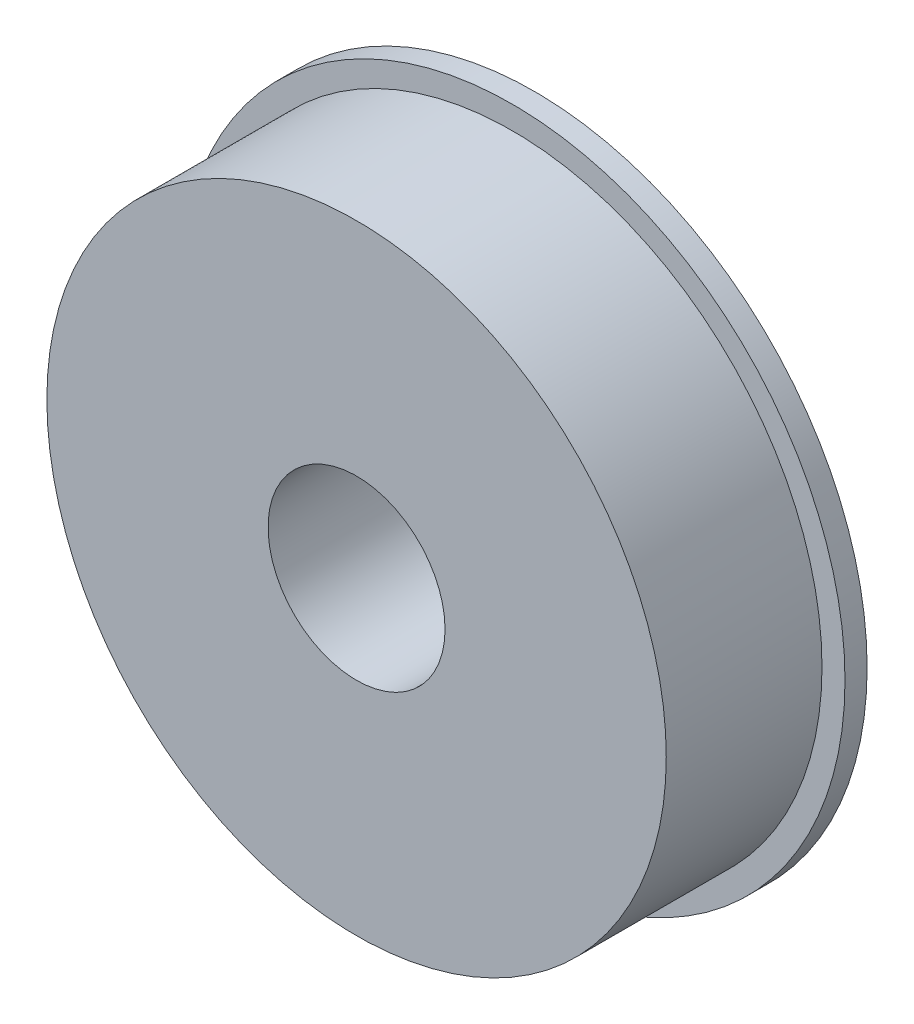
SolidWorks part; units mm, degrees
ref_plane "Front Plane" through (0, 0, 0) normal (0, 0, 1) x (1, 0, 0)
ref_plane "Top Plane" through (0, 0, 0) normal (0, 1, 0) x (1, 0, 0)
ref_plane "Right Plane" through (0, 0, 0) normal (1, 0, 0) x (0, 0, -1)
sketch "Sketch2" plane through (0, 0, 0) normal (0, 0, 1) x (1, 0, 0)
  circle A0 centre (0, 0) radius 23.876
  dimension "D1" = 47.752
extrude "Boss-Extrude1" add sketch "Sketch2" along normal blind 1.5875
sketch "Sketch3" plane through (0, 0, 1.5875) normal (0, 0, 1) x (1, 0, 0)
  circle A0 centre (0, 0) radius 22.225
  dimension "D1" = 44.45
extrude "Boss-Extrude2" add sketch "Sketch3" along normal blind 11.176
sketch "Sketch4" plane through (0, 0, 12.7635) normal (0, 0, 1) x (1, 0, 0)
  circle A0 centre (0, 0) radius 6.35
  dimension "D1" = 12.7
extrude "Cut-Extrude1" cut sketch "Sketch4" against normal blind 10.668
